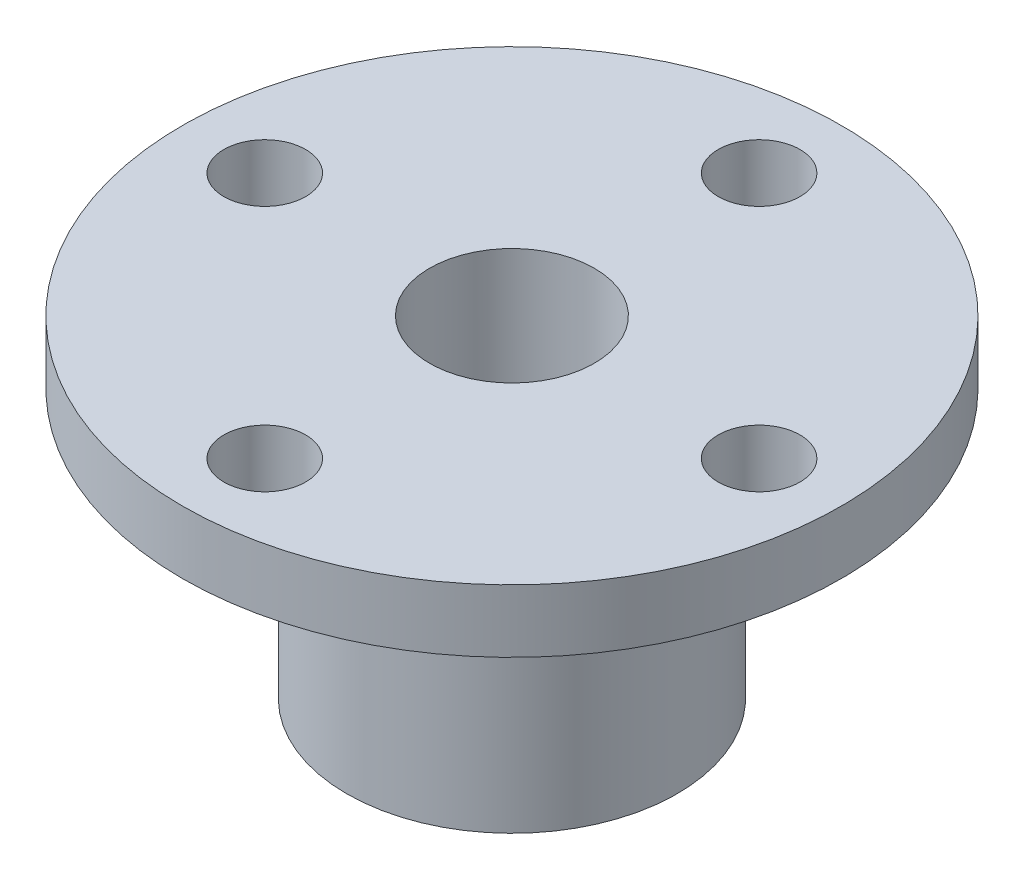
SolidWorks part; units mm, degrees
ref_plane "Front Plane" through (0, 0, 0) normal (0, 0, 1) x (1, 0, 0)
ref_plane "Top Plane" through (0, 0, 0) normal (0, 1, 0) x (1, 0, 0)
ref_plane "Right Plane" through (0, 0, 0) normal (1, 0, 0) x (0, 0, -1)
sketch "Sketch1" plane through (0, 0, 0) normal (0, 1, 0) x (1, 0, 0)
  circle A0 centre (0, 0) radius 4
  circle A1 centre (0, 0) radius 8.02
  dimension "D1" = 8
  dimension "D2" = 16.04
extrude "Boss-Extrude1" add sketch "Sketch1" along normal blind 13.04
sketch "Sketch2" plane through (0, 13.04, 0) normal (0, 1, 0) x (1, 0, 0)
  circle A0 centre (0, 0) radius 16
  dimension "D1" = 32
extrude "Boss-Extrude2" add sketch "Sketch2" along normal blind 3.05
sketch "Sketch3" plane through (0, 13.04, 0) normal (0, -1, 0) x (1, 0, 0)
  circle A0 centre (0, 0) radius 4
  dimension "D1" = 8
extrude "Cut-Extrude1" cut sketch "Sketch3" against normal through all
sketch "Sketch4" plane through (0, 16.09, 0) normal (0, 1, 0) x (1, 0, 0)
  line L0 (0, 16) -> (0, -16) construction
  line L1 (-16, 0) -> (16, 0) construction
  circle A0 centre (0, 0) radius 12 construction
  circle A1 centre (0, 0) radius 16 construction
  circle A2 centre (-12, 0) radius 1.985
  circle A3 centre (0, 12) radius 1.985
  circle A4 centre (12, 0) radius 1.985
  circle A5 centre (0, -12) radius 1.985
  dimension "D1" = 24
  dimension "D2" = 3.97
extrude "Cut-Extrude2" cut sketch "Sketch4" against normal through all
